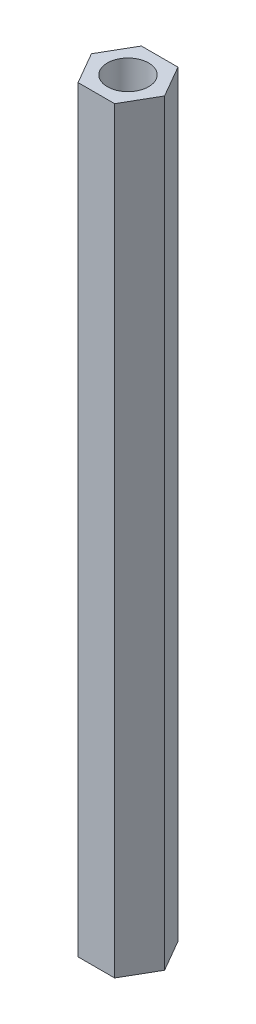
SolidWorks part; units mm, degrees
material "Brass"
ref_plane "Front Plane" through (0, 0, 0) normal (0, 0, 1) x (1, 0, 0)
ref_plane "Top Plane" through (0, 0, 0) normal (0, 1, 0) x (1, 0, 0)
ref_plane "Right Plane" through (0, 0, 0) normal (1, 0, 0) x (0, 0, -1)
sketch "Sketch1" plane through (0, 0, 0) normal (0, 1, 0) x (1, 0, 0)
  line L1 (1.3279, -2.3) -> (2.6558, 0)
  line L2 (2.6558, 0) -> (1.3279, 2.3)
  line L3 (1.3279, 2.3) -> (-1.3279, 2.3)
  line L4 (-1.3279, 2.3) -> (-2.6558, 0)
  line L5 (-2.6558, 0) -> (-1.3279, -2.3)
  line L6 (-1.3279, -2.3) -> (1.3279, -2.3)
  circle A0 centre (0, 0) radius 2.3 construction
  dimension "D1" = 4.6
extrude "Boss-Extrude1" add sketch "Sketch1" along normal blind 55
sketch "Sketch2" plane through (0, 55, 0) normal (0, 1, 0) x (1, 0, 0)
  circle A0 centre (0, 0) radius 1.5
  dimension "D1" = 3
extrude "Cut-Extrude1" cut sketch "Sketch2" against normal through all
